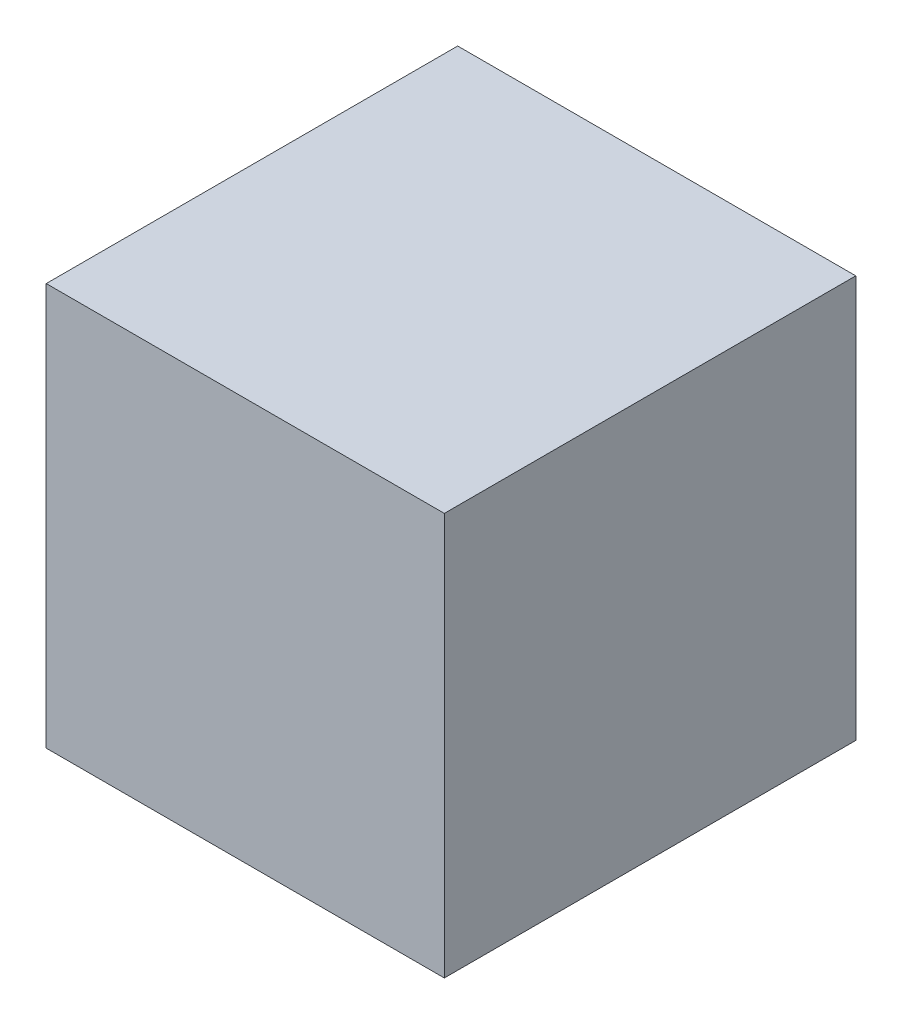
SolidWorks part; units mm, degrees
ref_plane "Front Plane" through (0, 0, 0) normal (0, 0, 1) x (1, 0, 0)
ref_plane "Top Plane" through (0, 0, 0) normal (0, 1, 0) x (1, 0, 0)
ref_plane "Right Plane" through (0, 0, 0) normal (1, 0, 0) x (0, 0, -1)
sketch "Sketch1" plane through (0, 0, 0) normal (0, 1, 0) x (1, 0, 0)
  line L1 (-78.724, 35.1987) -> (-41.1283, 35.1987)
  line L2 (-78.724, 35.1987) -> (-78.724, -3.6586)
  line L3 (-78.724, -3.6586) -> (-41.1283, -3.6586)
  line L4 (-41.1283, 35.1987) -> (-41.1283, -3.6586)
extrude "Boss-Extrude1" add sketch "Sketch1" along normal blind 38
